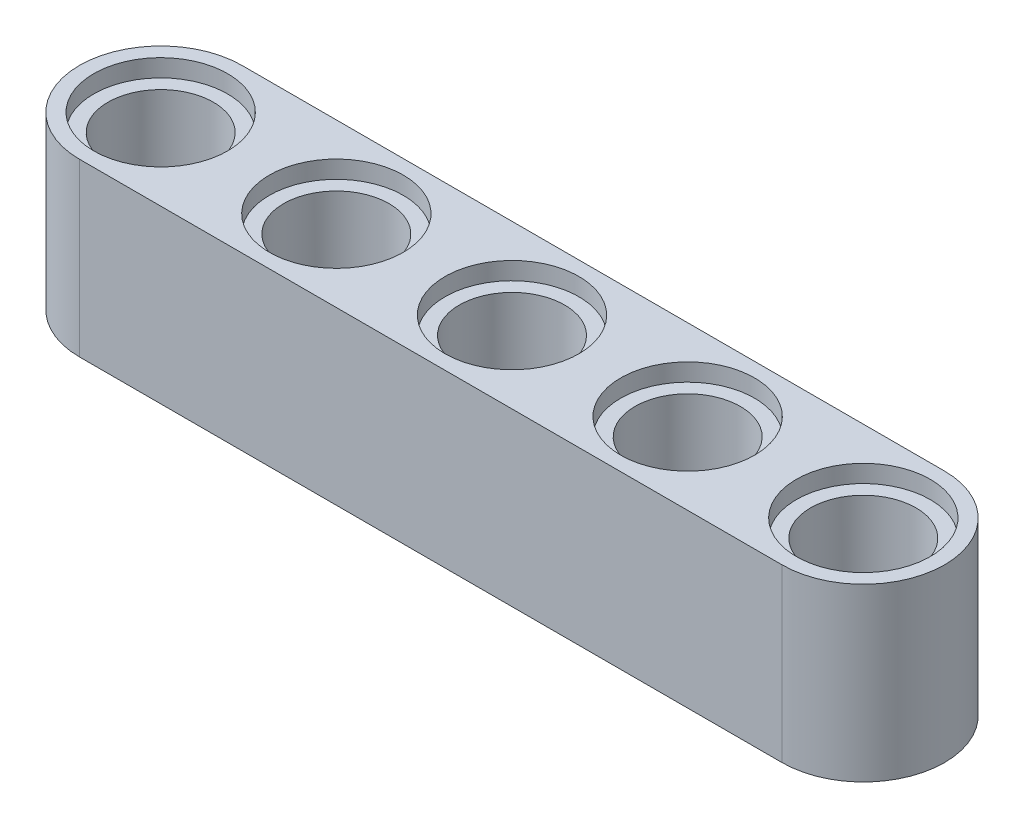
SolidWorks part; units mm, degrees
ref_plane "Front Plane" through (0, 0, 0) normal (0, 0, 1) x (1, 0, 0)
ref_plane "Top Plane" through (0, 0, 0) normal (0, 1, 0) x (1, 0, 0)
ref_plane "Right Plane" through (0, 0, 0) normal (1, 0, 0) x (0, 0, -1)
sketch "Sketch1" plane through (0, 0, 0) normal (0, 1, 0) x (1, 0, 0)
  line L0 (-16, -3.7) -> (16, -3.7)
  line L1 (-16, 3.7) -> (16, 3.7)
  arc A9 (16, 3.7) -> (16, -3.7) centre (16, 0) cw
  arc A10 (-16, 3.7) -> (-16, -3.7) centre (-16, 0) ccw
  point P0 (-19.7, 0)
  point P2 (19.7, 0)
  point P20 (8, -3.7)
  point P25 (-8, -3.7)
  dimension "D1" = 3.7
  dimension "D3" = 39.4
  dimension "D5" = 3.7
  dimension "D2" = 32
extrude "Boss-Extrude3" add sketch "Sketch1" along normal blind 7.8 contours A10 L0 A9 L1
sketch "Sketch2" plane through (0, 7.8, 0) normal (0, 1, 0) x (1, 0, 0)
  circle A0 centre (0, 0) radius 2.4
  circle A2 centre (8, 0) radius 2.4
  circle A5 centre (16, 0) radius 2.4
  circle A6 centre (-16, 0) radius 2.4
  circle A9 centre (-8, 0) radius 2.4
  dimension "D1" = 4.8
  dimension "D2" = 8
extrude "Cut-Extrude6" cut sketch "Sketch2" against normal blind 7.8 contours A6 | A9 | A0 | A2 | A5
sketch "Sketch3" plane through (0, 7.8, 0) normal (0, 1, 0) x (1, 0, 0)
  circle A0 centre (0, 0) radius 3.05
  circle A1 centre (8, 0) radius 3.05
  circle A2 centre (16, 0) radius 3.05
  circle A3 centre (-16, 0) radius 3.05
  circle A4 centre (-8, 0) radius 3.05
  dimension "D1" = 6.1
  dimension "D2" = 8
extrude "Cut-Extrude7" cut sketch "Sketch3" against normal blind 0.8
sketch "Sketch4" plane through (0, 0, 0) normal (0, -1, 0) x (1, 0, 0)
  circle A0 centre (0, 0) radius 3.05
  circle A1 centre (8, 0) radius 3.05
  circle A2 centre (16, 0) radius 3.05
  circle A3 centre (-16, 0) radius 3.05
  circle A4 centre (-8, 0) radius 3.05
  dimension "D1" = 6.1
  dimension "D2" = 8
extrude "Cut-Extrude8" cut sketch "Sketch4" against normal blind 0.8
